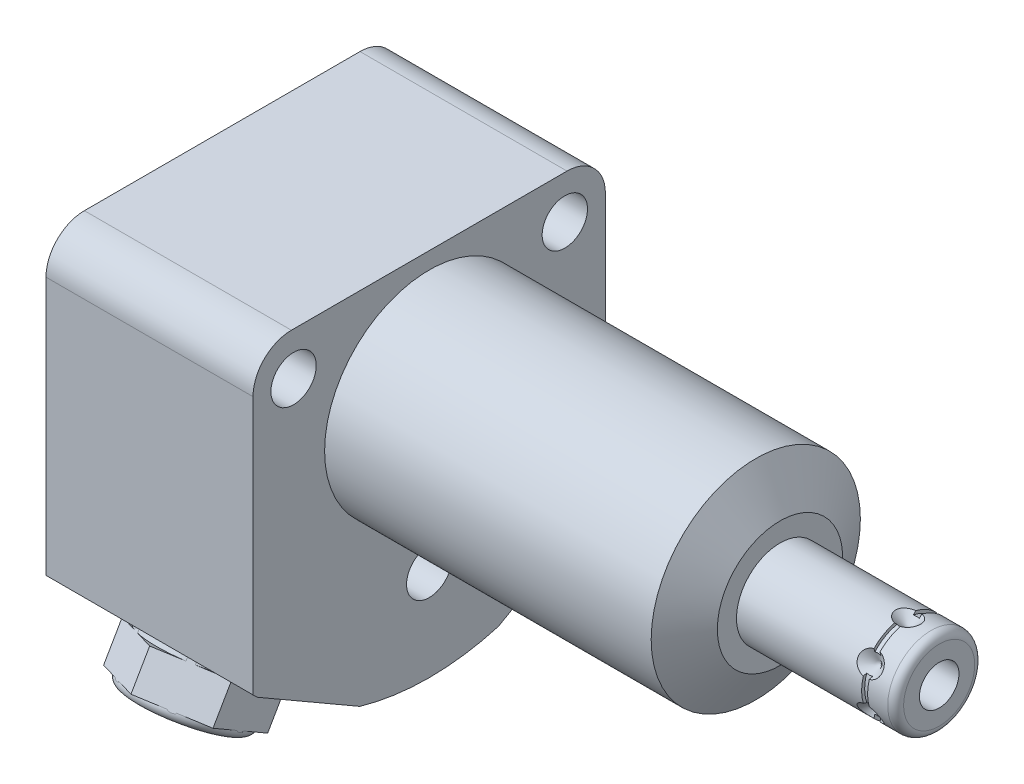
SolidWorks part; units mm, degrees
material "Alloy Steel"
ref_plane "Front Plane" through (0, 0, 0) normal (0, 0, 1) x (1, 0, 0)
ref_plane "Top Plane" through (0, 0, 0) normal (0, 1, 0) x (1, 0, 0)
ref_plane "Right Plane" through (0, 0, 0) normal (1, 0, 0) x (0, 0, -1)
sketch "Sketch1" plane through (0, 0, 0) normal (1, 0, 0) x (0, 0, -1)
  line L0 (-22.5044, 15.494) -> (-22.5044, -22.3968)
  line L1 (-21.968, -22.9231) -> (-8.868, -30.4864)
  line L2 (8.868, -30.4864) -> (21.968, -22.9231)
  line L3 (22.5044, -22.3968) -> (22.5044, 15.494)
  line L4 (22.5044, 15.494) -> (-22.5044, 15.494)
  line L5 (0, -34.1122) -> (0, 17.8562) construction
  line L6 (-36.4519, 0) -> (54.4719, 0) construction
  arc A0 (-8.868, -30.4864) -> (8.868, -30.4864) centre (0, 0) ccw
  arc A1 (-22.5044, -22.3968) -> (-21.968, -22.9231) centre (0, 0) ccw
  arc A2 (21.968, -22.9231) -> (22.5044, -22.3968) centre (0, 0) ccw
  dimension "D6" = 31.75
  dimension "D1" = 45.0088
  dimension "D2" = 30.836
  dimension "D3" = 45.0088
  dimension "D4" = 15.494
  dimension "D5" = 30
extrude "Extrude1" add sketch "Sketch1" along normal blind 44.8056 and the other way blind 26.4414
sketch "Sketch2" plane through (0, 0, 0) normal (1, 0, 0) x (0, 0, -1)
  line L6 (22.5044, 15.494) -> (-22.5044, 15.494)
  line L7 (-22.5044, 15.494) -> (-22.5044, -22.3968)
  line L8 (-21.968, -22.9231) -> (-8.868, -30.4864)
  line L9 (8.868, -30.4864) -> (21.968, -22.9231)
  line L10 (22.5044, -22.3968) -> (22.5044, 15.494)
  line L11 (22.5044, 15.494) -> (-22.5044, 15.494)
  line L12 (-22.5044, 15.494) -> (-22.5044, -22.3968)
  line L13 (-21.968, -22.9231) -> (-8.868, -30.4864)
  line L14 (8.868, -30.4864) -> (21.968, -22.9231)
  line L15 (22.5044, -22.3968) -> (22.5044, 15.494)
  circle A0 centre (0, 0) radius 13.3604
  arc A4 (-22.5044, -22.3968) -> (-21.968, -22.9231) centre (0, 0) ccw
  arc A5 (-8.868, -30.4864) -> (8.868, -30.4864) centre (0, 0) ccw
  arc A6 (21.968, -22.9231) -> (22.5044, -22.3968) centre (0, 0) ccw
  arc A7 (-22.5044, -22.3968) -> (-21.968, -22.9231) centre (0, 0) ccw
  arc A8 (-8.868, -30.4864) -> (8.868, -30.4864) centre (0, 0) ccw
  arc A9 (21.968, -22.9231) -> (22.5044, -22.3968) centre (0, 0) ccw
  dimension "D2" = 26.7208
  dimension "D1" = 0
extrude "Cut-Extrude1" cut sketch "Sketch2" along normal up to next
sketch "Sketch3" plane through (0, 0, 0) normal (0, 0, 1) x (1, 0, 0)
  line L0 (41.7113, 13.3604) -> (44.8056, 8.001)
  line L1 (23.3045, 0) -> (44.9603, 0) construction
  line L2 (44.8056, 13.3604) -> (44.8056, 8.001)
  line L3 (44.8056, 13.3604) -> (41.7113, 13.3604)
  line L4 (44.8056, -13.3604) -> (44.8056, 13.3604) construction
  line L5 (44.8056, 13.3604) -> (0, 13.3604) construction
  dimension "D1" = 30
  dimension "D2" = 16.002
revolve "Cut-Revolve1" cut sketch "Sketch3" angle 360 about L1
ref_plane "Plane19" through (0, 0, 10.49) normal (0, 0, 1) x (1, 0, 0)
sketch "S2D0002" plane through (-24.9936, -18.1864, 10.49) normal (0, 0, 1) x (0, 1, 0)
  line L0 (3.2512, 0) -> (5.7023, 0)
  line L1 (3.2512, 0) -> (3.2512, -2.9972)
  line L2 (3.2512, -2.9972) -> (1.2446, -2.9972)
  line L3 (1.2446, -2.9972) -> (1.2446, -11.9888)
  line L4 (1.2446, -11.9888) -> (0, -11.9888)
  line L5 (0, -11.9888) -> (0, 1.4478)
  line L6 (0, -23.5585) -> (0, 0.5994) construction
  line L7 (5.7023, 0) -> (5.7023, 1.4478)
  line L8 (33.6804, 1.4478) -> (-4.2104, 1.4478) construction
  line L9 (5.7023, 1.4478) -> (0, 1.4478)
  dimension "D1" = 1.4478
  dimension "D2" = 18.1864
  dimension "D3" = 11.4046
  dimension "D4" = 6.5024
  dimension "D5" = 2.4892
  dimension "D6" = 8.9916
  dimension "D7" = 2.9972
revolve "Cut-Revolve2" cut sketch "S2D0002" angle 360 about L6
ref_plane "Plane20" through (-12.9286, 0, 0) normal (1, 0, 0) x (0, 0, -1)
sketch "Sketch6" plane through (-12.9286, 0, 0) normal (1, 0, 0) x (0, 0, -1)
  line L0 (-19.5804, -24.0083) -> (-22.4357, -22.3598)
  line L1 (-19.5804, -24.0083) -> (-19.5169, -23.8983)
  line L2 (-19.5169, -23.8983) -> (-18.7883, -23.7031)
  line L3 (-18.7883, -23.7031) -> (-13.8353, -15.1242)
  line L4 (-13.8353, -15.1242) -> (-10.0078, -17.334)
  line L5 (-10.0078, -17.334) -> (-15.418, -26.7048)
  line L6 (-6.5499, -11.3447) -> (3.1494, 5.455) construction
  line L7 (-22.4357, -22.3598) -> (-22.5627, -22.5798)
  line L8 (-21.968, -22.9231) -> (-8.868, -30.4864) construction
  line L9 (-22.5627, -22.5798) -> (-15.418, -26.7048)
  line L10 (-21.968, -22.9231) -> (-8.868, -30.4864) construction
  dimension "D1" = 0.254
  dimension "D2" = 16.5
  dimension "D3" = 45
  dimension "D4" = 0.6604
  dimension "D5" = 9.906
  dimension "D6" = 8.8392
  dimension "D7" = 10.5664
  dimension "D8" = 0.127
revolve "Cut-Revolve4" cut sketch "Sketch6" angle 360 about L6
mirror "Mirror1" about plane through (0, 0, 0) normal (0, 0, 1) of "Cut-Revolve2", "Cut-Revolve4"
sketch "Sketch7" plane through (0, 0, 0) normal (0, 0, 1) x (1, 0, 0)
  line L0 (44.8056, 0) -> (44.8056, 5.5563)
  line L1 (44.8056, 5.5563) -> (64.1226, 5.5563)
  line L2 (65.1386, 4.5403) -> (65.1386, 0)
  line L3 (65.1386, 0) -> (44.8056, 0)
  line L4 (4.9931, 0) -> (66.1154, 0) construction
  line L5 (44.8056, -8.001) -> (44.8056, 8.001) construction
  line L6 (-26.4414, 15.494) -> (-26.4414, -22.3968) construction
  arc A0 (65.1386, 4.5403) -> (64.1226, 5.5563) centre (64.1226, 4.5403) ccw
  point P0 (44.8056, 0)
  dimension "D3" = 1.016
  dimension "D1" = 91.58
  dimension "D2" = 11.1125
revolve "Revolve1" add sketch "Sketch7" angle 360 about L4
sketch "S2D0001" plane through (0, 0, 0) normal (0, 0, 1) x (1, 0, 0)
  line L0 (65.1386, -2.5273) -> (54.9786, -2.5273)
  line L1 (54.9786, -2.5273) -> (53.46, 0)
  line L2 (65.1386, -2.5273) -> (65.1386, 0)
  line L3 (65.1386, 0) -> (53.46, 0)
  line L4 (-2.5273, 0) -> (-28.8062, 0) construction
  line L5 (65.1386, -4.5403) -> (65.1386, 4.5403) construction
  dimension "D1" = 5.0546
  dimension "D2" = 10.16
  dimension "D3" = 59
revolve "Cut-Revolve8" cut sketch "S2D0001" angle 360 about L4
sketch "Sketch9" plane through (0, 0, 0) normal (0, 0, 1) x (1, 0, 0)
  line L0 (61.1762, -5.5563) -> (59.5887, -5.5563)
  line L1 (59.5887, -5.5563) -> (61.1762, -3.9688)
  line L2 (61.1762, -5.5563) -> (61.1762, -3.9688)
  line L3 (61.1762, -6.2534) -> (61.1762, 0.0794) construction
  line L4 (44.8056, -5.5563) -> (64.1226, -5.5563) construction
  line L5 (65.1386, -4.5403) -> (65.1386, 4.5403) construction
  dimension "D1" = 3.9624
  dimension "D2" = 45
  dimension "D3" = 3.175
revolve "Cut-Revolve9" cut sketch "Sketch9" angle 360 about L3
sketch "Sketch11" plane through (0, 0, 0) normal (0, 1, 0) x (1, 0, 0)
  line L0 (61.5572, -5.5563) -> (61.5572, -5.1753)
  line L1 (61.5572, -5.1753) -> (60.7952, -5.1753)
  line L2 (60.7952, -5.1753) -> (60.7952, -5.5563)
  line L3 (60.7952, -5.5563) -> (61.5572, -5.5563)
  line L4 (0, 0) -> (83.4312, 0) construction
  line L6 (44.8056, -5.5563) -> (64.1226, -5.5563) construction
  line L7 (61.1762, 0) -> (61.1762, -20.2865) construction
  dimension "D1" = 0.762
  dimension "D2" = 0.381
revolve "Cut-Revolve5" cut sketch "Sketch11" angle 360 about L4
sketch "Sketch12" plane through (0, -26.4848, 15.291) normal (0, -0.866, 0.5) x (1, 0, 0)
  line L8 (-12.9286, -8.0656) -> (-5.9436, -4.0328)
  line L9 (-5.9436, -4.0328) -> (-5.9436, 4.0328)
  line L10 (-5.9436, 4.0328) -> (-12.9286, 8.0656)
  line L11 (-12.9286, 8.0656) -> (-19.9136, 4.0328)
  line L12 (-19.9136, 4.0328) -> (-19.9136, -4.0328)
  line L13 (-19.9136, -4.0328) -> (-12.9286, -8.0656)
  circle A0 centre (-12.9286, 0) radius 6.985 construction
  dimension "D2" = 13.97
extrude "Extrude2" add sketch "Sketch12" along normal blind 6.78
sketch "Sketch13" plane through (-12.9286, -6.4643, -11.1965) normal (1, 0, 0) x (0, -0.866, 0.5)
  line L0 (30.582, -5.9286) -> (31.582, -5.9286)
  line L1 (31.582, -5.9286) -> (31.582, -4.6786)
  line L2 (31.582, -4.6786) -> (30.582, -4.6786)
  line L3 (30.582, -4.6786) -> (30.582, -5.9286)
  line L4 (36.362, -5.9286) -> (36.362, -4.6786)
  line L5 (36.362, -4.6786) -> (37.362, -4.6786)
  line L6 (37.362, -4.6786) -> (37.362, -6.9286)
  line L7 (30.082, -12.9286) -> (41.082, -12.9286) construction
  line L8 (20.0156, -12.9286) -> (29.9216, -12.9286) construction
  line L9 (37.362, -16.9614) -> (37.362, -20.9942) construction
  line L11 (30.582, -16.9614) -> (30.582, -20.9942) construction
  arc A0 (37.362, -6.9286) -> (36.362, -5.9286) centre (36.362, -6.9286) ccw
  dimension "D3" = 1
  dimension "D1" = 1
  dimension "D2" = 16.5
  dimension "D4" = 1
  dimension "D5" = 16.5
  dimension "D6" = 14
revolve "Cut-Revolve6" cut sketch "Sketch13" angle 360 about L7
sketch "Sketch15" plane through (-21.9964, 0, 0) normal (-1, 0, 0) x (0, 0, 1)
  circle A0 centre (10.49, -18.1864) radius 2.7432
  circle A1 centre (10.49, -18.1864) radius 3.2512 construction
  dimension "D1" = 5.4864
extrude "Extrude3" add sketch "Sketch15" along normal blind 2.9972
sketch "Sketch16" plane through (-24.9936, 0, 0) normal (-1, 0, 0) x (0, 0, 1)
  line L7 (11.9271, -18.1864) -> (11.2086, -16.9418)
  line L8 (11.2086, -16.9418) -> (9.7714, -16.9418)
  line L9 (9.7714, -16.9418) -> (9.0529, -18.1864)
  line L10 (9.0529, -18.1864) -> (9.7714, -19.431)
  line L11 (9.7714, -19.431) -> (11.2086, -19.431)
  line L12 (11.2086, -19.431) -> (11.9271, -18.1864)
  circle A0 centre (10.49, -18.1864) radius 1.2446 construction
  dimension "D1" = 2.4892
extrude "Cut-Extrude2" cut sketch "Sketch16" against normal blind 2.54
chamfer "Chamfer1" distance 0.381 angle 45 1 edges at (-24.9936, -18.1864, 13.2332)
mirror "Mirror2" about plane through (0, 0, 0) normal (0, 0, 1) of "Extrude3", "Cut-Extrude2", "Chamfer1"
sketch "Sketch21" plane through (0, 0, 10.49) normal (0, 0, 1) x (1, 0, 0)
  line L0 (-35.9744, -18.1864) -> (-17.6399, -18.1864) construction
  line L1 (-13.0048, -16.9418) -> (-21.9964, -16.9418) construction
  line L2 (-21.9964, -19.431) -> (-17.3029, -19.431) construction
  line L3 (-24.9936, -12.4841) -> (-24.9936, -23.8887) construction
  circle A0 centre (-25.8572, -13.3731) radius 0.889
  dimension "D1" = 1.778
  dimension "D2" = 9.6266
  dimension "D3" = 0.8636
revolve "Revolve4" add sketch "Sketch21" angle 360 about L0
mirror "Mirror3" about plane through (0, 0, 0) normal (0, 0, 1) of bodies 129
fillet "Fillet1" radius 4.9022 2 edges at (-13.2207, 15.494, 22.5044) (-13.2207, 15.494, -22.5044)
hole_wizard "Hole1" positions "Sketch23" profile "Sketch22" legacy end condition up to next
sketch "Sketch23" plane through (0, 0, 0) normal (1, 0, 0) x (0, 0, -1)
  line L0 (0, 0) -> (0, 19.8912) construction
  point P0 (0, -19.9898)
  point P5 (-17.3228, 10.0076)
  point P13 (17.3228, 10.0076)
  dimension "D1" = 19.9898
  dimension "D2" = 10.0076
  dimension "D3" = 17.3228
sketch "Sketch22" plane through (0, -19.9898, 0) normal (0, 1, 0) x (0, 0, -1)
  line L0 (0, 0) -> (0, 26.4414)
  line L1 (0, 26.4414) -> (2.8955, 26.4414)
  line L2 (2.8955, 26.4414) -> (2.8955, 0)
  line L3 (2.8955, 0) -> (0, 0)
  line L4 (0, 110) -> (0, -10) construction
  dimension "Diameter" = 5.791
  dimension "Depth" = 26.4414
pattern_circular "CirPattern1" count 6 over 360 about axis through (0, 0, 0) along (1, 0, 0) of "Cut-Revolve9"
